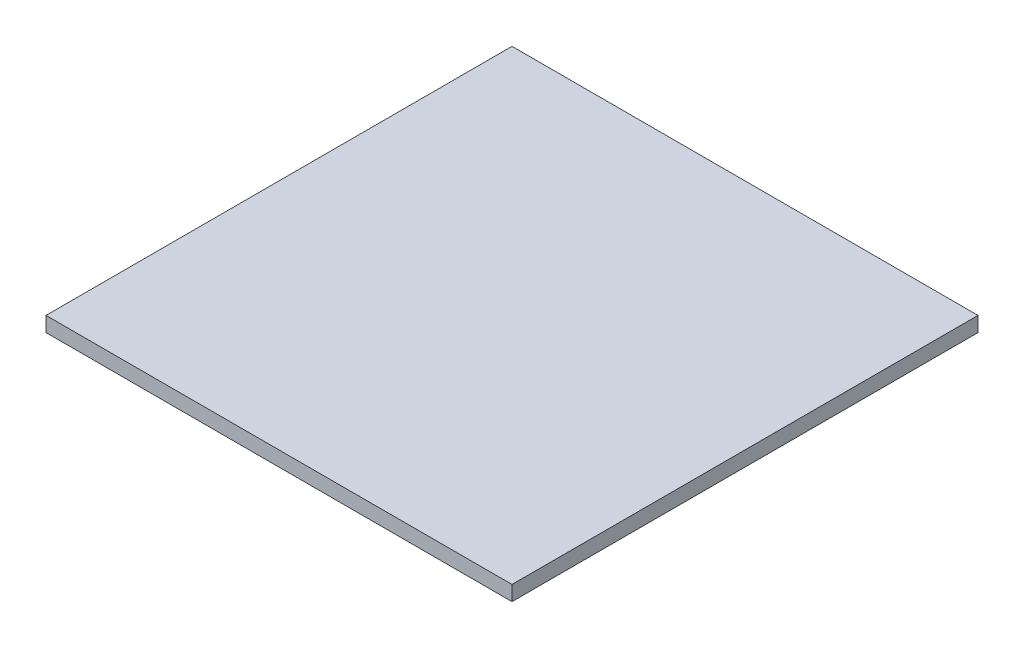
SolidWorks part; units mm, degrees
ref_plane "Front Plane" through (0, 0, 0) normal (0, 0, 1) x (1, 0, 0)
ref_plane "Top Plane" through (0, 0, 0) normal (0, 1, 0) x (1, 0, 0)
ref_plane "Right Plane" through (0, 0, 0) normal (1, 0, 0) x (0, 0, -1)
sketch "Sketch1" plane through (0, 0, 0) normal (0, 1, 0) x (1, 0, 0)
  line L1 (-25, 25) -> (25, 25)
  line L2 (-25, 25) -> (-25, -25)
  line L3 (-25, -25) -> (25, -25)
  line L4 (25, 25) -> (25, -25)
  line L5 (-25, 25) -> (25, -25) construction
  line L6 (-25, -25) -> (25, 25) construction
  point P0 (0, 0)
  dimension "D1" = 50
  dimension "D2" = 50
extrude "Boss-Extrude1" add sketch "Sketch1" along normal blind 1.6
